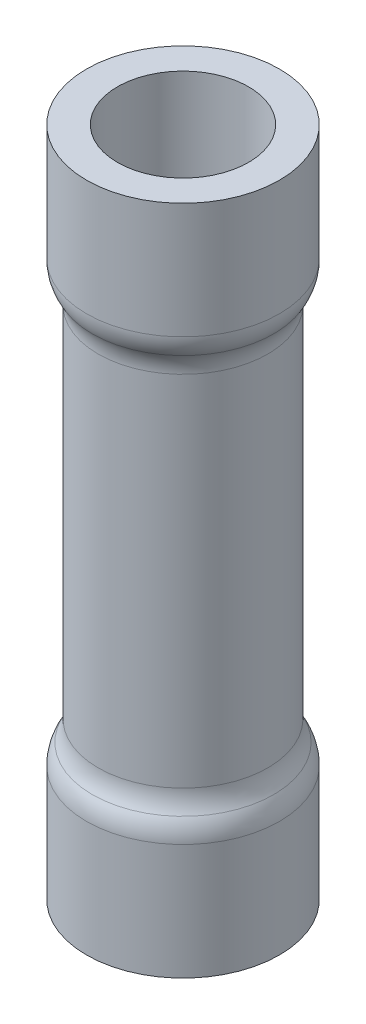
SolidWorks part; units mm, degrees
material "PVC 0.007 Plasticized"
ref_plane "Front Plane" through (0, 0, 0) normal (0, 0, 1) x (1, 0, 0)
ref_plane "Top Plane" through (0, 0, 0) normal (0, 1, 0) x (1, 0, 0)
ref_plane "Right Plane" through (0, 0, 0) normal (1, 0, 0) x (0, 0, -1)
sketch "Sketch1" plane through (0, 0, 0) normal (0, 0, 1) x (1, 0, 0)
  line L0 (2.794, 16.95) -> (2.794, 5.148)
  line L1 (3.175, 0) -> (3.175, 3.81)
  line L2 (0, 11.049) -> (3.175, 11.049) construction
  line L3 (3.175, 18.288) -> (3.175, 22.098)
  line L5 (0, 22.098) -> (0, 0) construction
  arc A0 (3.175, 3.81) -> (2.9845, 4.479) centre (1.905, 3.81) ccw
  arc A1 (2.9845, 4.479) -> (2.794, 5.148) centre (4.064, 5.148) cw
  arc A2 (3.175, 18.288) -> (2.9845, 17.619) centre (1.905, 18.288) cw
  arc A3 (2.9845, 17.619) -> (2.794, 16.95) centre (4.064, 16.95) ccw
  dimension "D5" = 1.27
  dimension "D1" = 22.098
  dimension "D2" = 3.175
  dimension "D3" = 0.381
  dimension "D4" = 3.81
revolve "Revolve-Thin1" add sketch "Sketch1" angle 360 about L5
